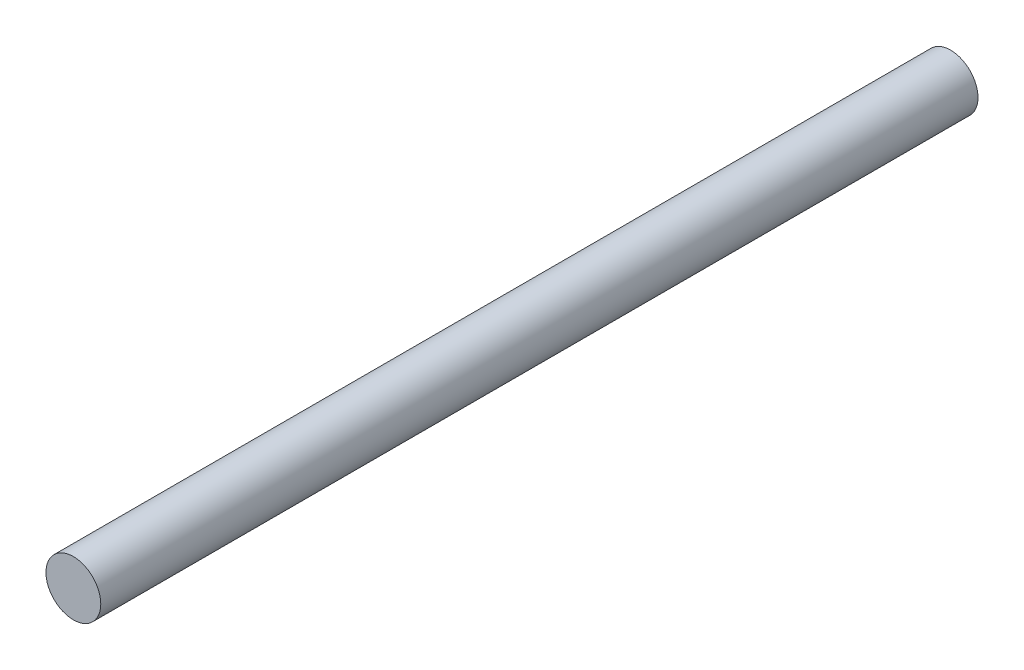
SolidWorks part; units mm, degrees
ref_plane "Front Plane" through (0, 0, 0) normal (0, 0, 1) x (1, 0, 0)
ref_plane "Top Plane" through (0, 0, 0) normal (0, 1, 0) x (1, 0, 0)
ref_plane "Right Plane" through (0, 0, 0) normal (1, 0, 0) x (0, 0, -1)
sketch "Sketch1" plane through (0, 0, 0) normal (0, 0, 1) x (1, 0, 0)
  circle A0 centre (0, 0) radius 2.3813
  dimension "D1" = 4.7625
extrude "Boss-Extrude1" add sketch "Sketch1" along normal mid plane 76.2
